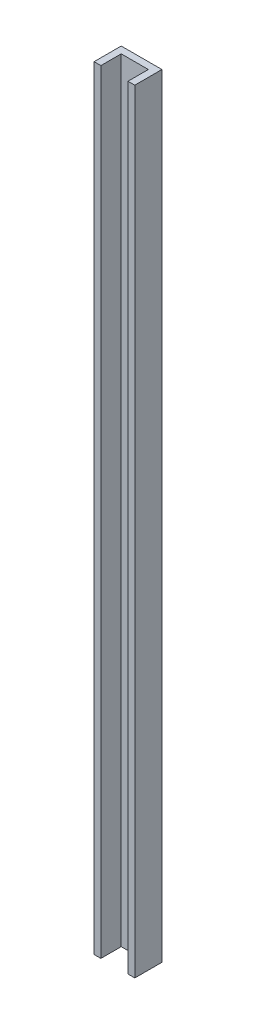
SolidWorks part; units mm, degrees
material "Plain Carbon Steel"
ref_plane "Front Plane" through (0, 0, 0) normal (0, 0, 1) x (1, 0, 0)
ref_plane "Top Plane" through (0, 0, 0) normal (0, 1, 0) x (1, 0, 0)
ref_plane "Right Plane" through (0, 0, 0) normal (1, 0, 0) x (0, 0, -1)
sketch "Sketch1" plane through (0, 0, 0) normal (0, 1, 0) x (1, 0, 0)
  line L0 (0, 0) -> (0, 12.7)
  line L1 (0, 12.7) -> (19.05, 12.7)
  line L2 (19.05, 12.7) -> (19.05, 0)
  line L3 (19.05, 0) -> (15.875, 0)
  line L4 (15.875, 0) -> (15.875, 9.525)
  line L5 (15.875, 9.525) -> (3.175, 9.525)
  line L6 (3.175, 9.525) -> (3.175, 0)
  line L7 (3.175, 0) -> (0, 0)
extrude "Boss-Extrude1" add sketch "Sketch1" along normal blind 361.95
